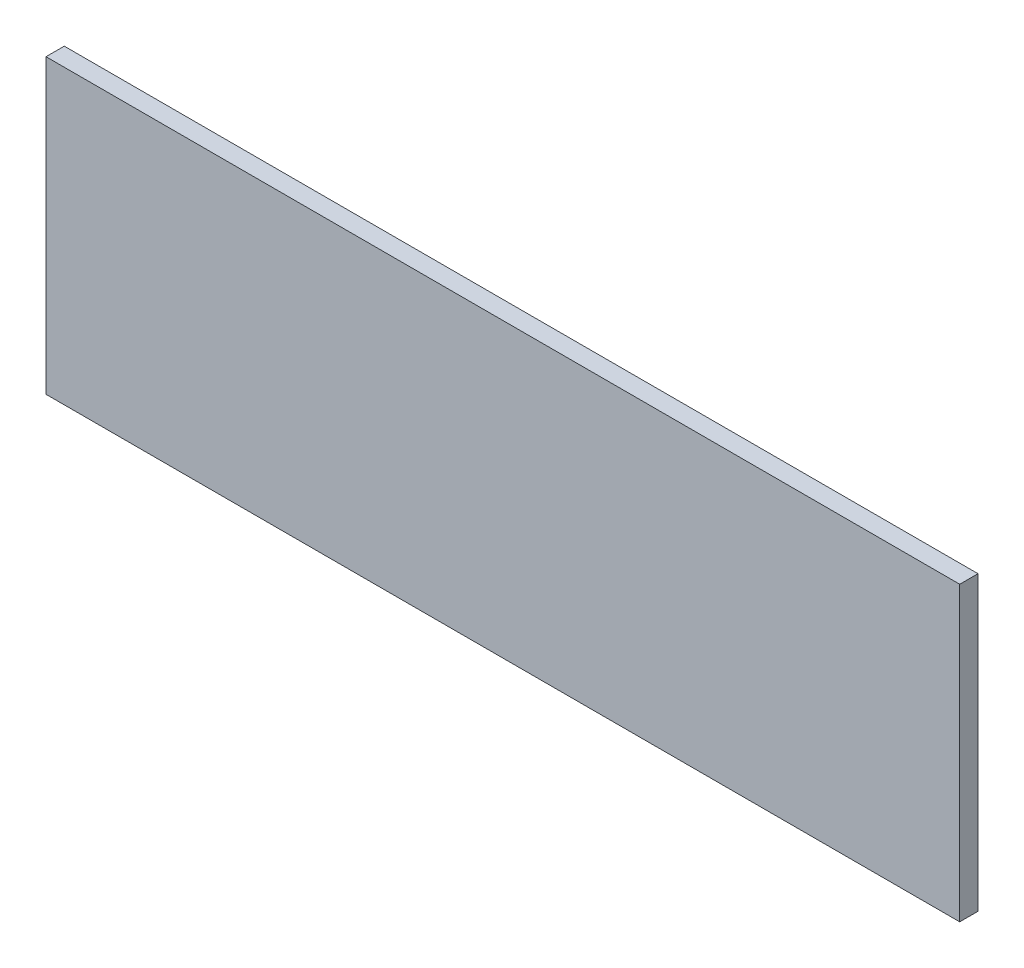
SolidWorks part; units mm, degrees
ref_plane "Front Plane" through (0, 0, 0) normal (0, 0, 1) x (1, 0, 0)
ref_plane "Top Plane" through (0, 0, 0) normal (0, 1, 0) x (1, 0, 0)
ref_plane "Right Plane" through (0, 0, 0) normal (1, 0, 0) x (0, 0, -1)
sketch "Sketch1" plane through (0, 0, 0) normal (0, 0, 1) x (1, 0, 0)
  line L1 (-317.5, -101.6) -> (317.5, -101.6)
  line L2 (-317.5, -101.6) -> (-317.5, 101.6)
  line L3 (-317.5, 101.6) -> (317.5, 101.6)
  line L4 (317.5, -101.6) -> (317.5, 101.6)
  line L5 (-317.5, -101.6) -> (317.5, 101.6) construction
  line L6 (-317.5, 101.6) -> (317.5, -101.6) construction
  point P0 (0, 0)
  dimension "D1" = 635
  dimension "D2" = 203.2
extrude "Boss-Extrude1" add sketch "Sketch1" along normal blind 12.7
